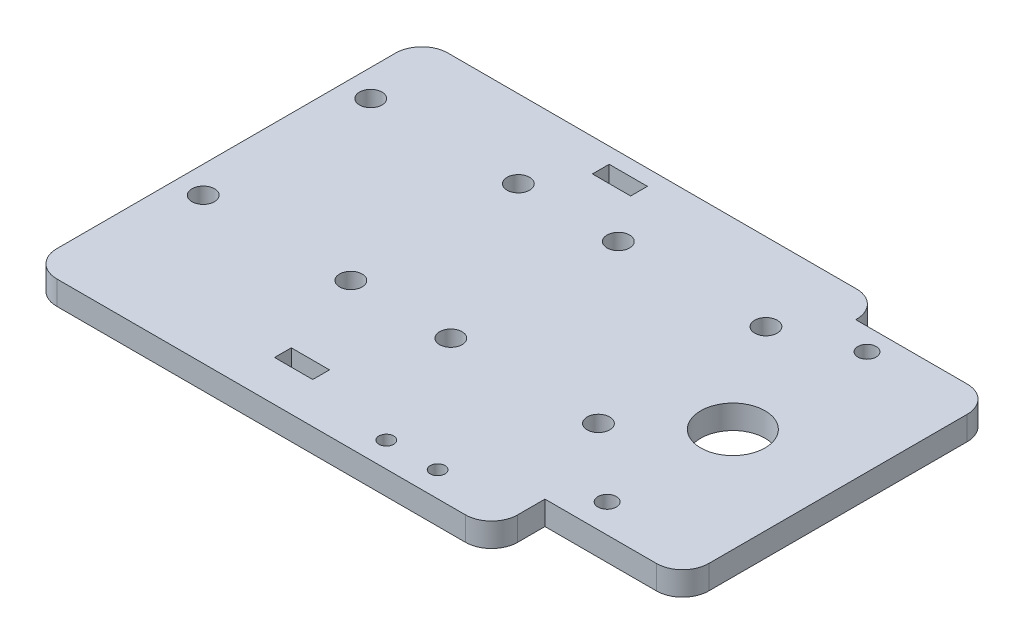
SolidWorks part; units mm, degrees
ref_plane "Front Plane" through (0, 0, 0) normal (0, 0, 1) x (1, 0, 0)
ref_plane "Top Plane" through (0, 0, 0) normal (0, 1, 0) x (1, 0, 0)
ref_plane "Right Plane" through (0, 0, 0) normal (1, 0, 0) x (0, 0, -1)
sketch "Sketch1" plane through (0, 0, 0) normal (0, 1, 0) x (1, 0, 0)
  line L1 (5, 0) -> (83.06, 0)
  line L2 (0, 5) -> (0, 69.73)
  line L3 (5, 74.73) -> (83.06, 74.73)
  line L4 (114.36, 15.2) -> (114.36, 64.57)
  line L5 (88.06, 69.57) -> (109.36, 69.57)
  line L6 (88.06, 69.57) -> (88.06, 69.73)
  line L11 (109.36, 10.2) -> (88.06, 10.2)
  line L12 (88.06, 5) -> (88.06, 10.2)
  line L13 (38.8, 71.73) -> (46.1, 71.73)
  line L14 (38.8, 71.73) -> (38.8, 68.53)
  line L15 (38.8, 68.53) -> (46.1, 68.53)
  line L16 (46.1, 71.73) -> (46.1, 68.53)
  line L17 (38.8, 11) -> (46.1, 11)
  line L18 (38.8, 11) -> (38.8, 7.8)
  line L19 (38.8, 7.8) -> (46.1, 7.8)
  line L20 (46.1, 11) -> (46.1, 7.8)
  circle A0 centre (5.15, 59.83) radius 2.15
  circle A1 centre (33.35, 59.83) radius 2.15
  circle A2 centre (52.45, 59.83) radius 2.15
  circle A3 centre (80.65, 59.83) radius 2.15
  circle A8 centre (5.15, 27.83) radius 2.15
  circle A9 centre (33.35, 27.83) radius 2.15
  circle A10 centre (52.45, 27.83) radius 2.15
  circle A11 centre (80.65, 27.83) radius 2.15
  arc A12 (88.06, 69.73) -> (83.06, 74.73) centre (83.06, 69.73) ccw
  arc A13 (109.36, 69.57) -> (114.36, 64.57) centre (109.36, 64.57) cw
  arc A14 (114.36, 15.2) -> (109.36, 10.2) centre (109.36, 15.2) cw
  arc A15 (83.06, 0) -> (88.06, 5) centre (83.06, 5) ccw
  arc A16 (5, 0) -> (0, 5) centre (5, 5) cw
  arc A17 (0, 69.73) -> (5, 74.73) centre (5, 69.73) cw
  circle A18 centre (94.47, 39.69) radius 6.15
  circle A19 centre (94.45, 65.33) radius 1.75
  circle A20 centre (94.45, 15.69) radius 1.75
  circle A21 centre (63.15, 4.8) radius 1.4
  circle A22 centre (72.95, 4.8) radius 1.4
  point P27 (88.06, 74.73)
  point P30 (114.36, 69.57)
  point P33 (114.36, 10.2)
  point P36 (88.06, 0)
  point P39 (0, 0)
  point P42 (0, 74.73)
  point P61 (0, 0)
  point P62 (0, 0)
  point P63 (64.0829, 4.4408)
  point P64 (0, 0)
  dimension "D3" = 4.3
  dimension "D4" = 4.3
  dimension "D5" = 4.3
  dimension "D6" = 4.3
  dimension "D19" = 5
  dimension "D28" = 12.3
  dimension "D31" = 3.5
  dimension "D32" = 3.5
  dimension "D37" = 2.8
  dimension "D38" = 2.8
  dimension "D1" = 74.73
  dimension "D8" = 14.9
  dimension "D9" = 14.9
  dimension "D10" = 14.9
  dimension "D7" = 14.9
  dimension "D11" = 28.2
  dimension "D12" = 28.2
  dimension "D13" = 19.1
  dimension "D14" = 5.15
  dimension "D16" = 5.16
  dimension "D17" = 26.3
  dimension "D2" = 26.3
  dimension "D18" = 10.2
  dimension "D20" = 7.3
  dimension "D21" = 3.2
  dimension "D22" = 38.8
  dimension "D23" = 7.8
  dimension "D24" = 7.3
  dimension "D25" = 3.2
  dimension "D26" = 0
  dimension "D27" = 3
  dimension "D29" = 19.89
  dimension "D30" = 29.88
  dimension "D34" = 94.45
  dimension "D35" = 9.4
  dimension "D36" = 49.64
  dimension "D33" = 0
  dimension "D39" = 4.8
  dimension "D40" = 4.8
  dimension "D41" = 9.8
  dimension "D42" = 15.11
  dimension "D15" = 2
extrude "Boss-Extrude1" add sketch "Sketch1" along normal blind 4.55
equation "\"D4@Sketch1\"=\"D3@Sketch1\""
equation "\"D5@Sketch1\"=\"D4@Sketch1\""
equation "\"D6@Sketch1\"=\"D3@Sketch1\""
equation "\"D8@Sketch1\"=\"D7@Sketch1\""
equation "\"D9@Sketch1\"=\"D7@Sketch1\""
equation "\"D10@Sketch1\"=\"D7@Sketch1\""
equation "\"D12@Sketch1\"=\"D11@Sketch1\""
equation "\"D24@Sketch1\"=\"D20@Sketch1\""
equation "\"D25@Sketch1\"=\"D21@Sketch1\""
equation "\"D40@Sketch1\"=\"D39@Sketch1\""
